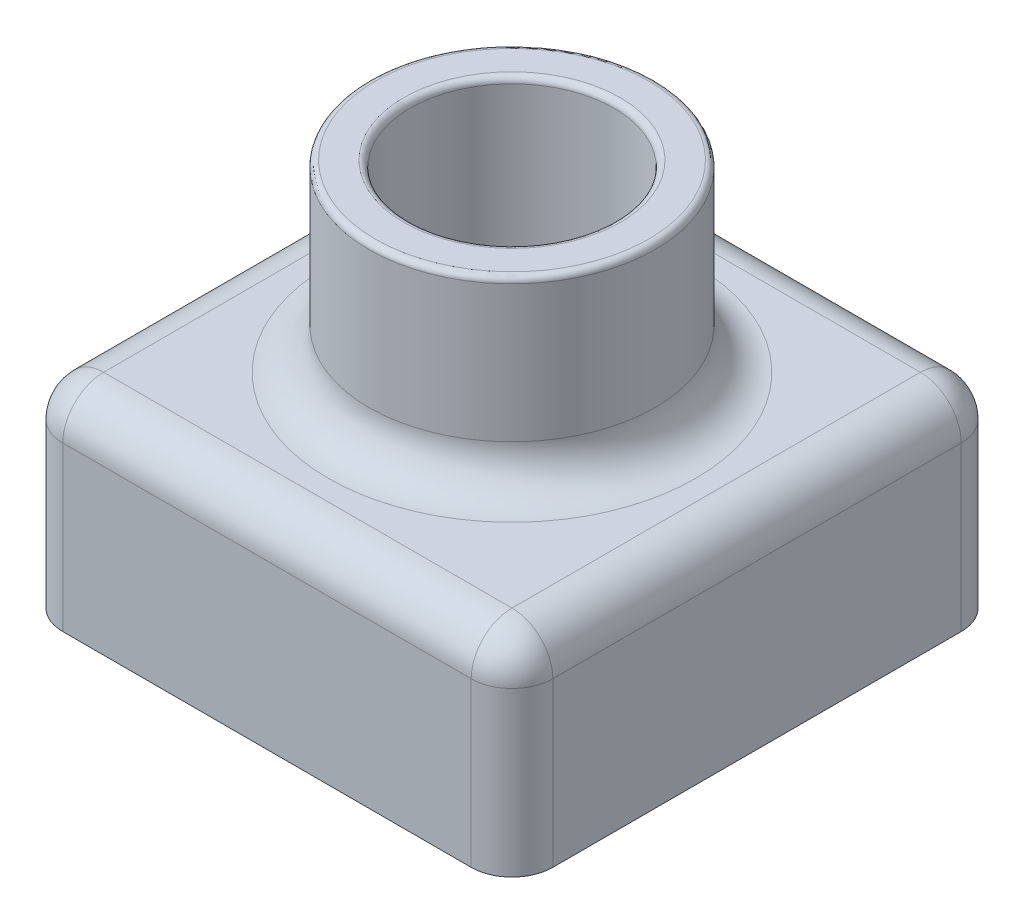
SolidWorks part; units mm, degrees
ref_plane "Front Plane" through (0, 0, 0) normal (0, 0, 1) x (1, 0, 0)
ref_plane "Top Plane" through (0, 0, 0) normal (0, 1, 0) x (1, 0, 0)
ref_plane "Right Plane" through (0, 0, 0) normal (1, 0, 0) x (0, 0, -1)
sketch "Sketch3" plane through (0, 0, 0) normal (0, 1, 0) x (1, 0, 0)
  line L1 (0, 0) -> (120, 0)
  line L2 (0, 0) -> (0, 120)
  line L3 (0, 120) -> (120, 120)
  line L4 (120, 0) -> (120, 120)
  dimension "D1" = 120
  dimension "D2" = 120
extrude "Boss-Extrude2" add sketch "Sketch3" along normal blind 50 contours L2 L1 L4 L3
sketch "Sketch4" plane through (0, 50, 0) normal (0, 1, 0) x (1, 0, 0)
  line L0 (0, 120) -> (120, 120) construction
  line L1 (120, 0) -> (120, 120) construction
  circle A0 centre (60, 60) radius 35
  dimension "D1" = 70
  dimension "D2" = 60
  dimension "D3" = 60
extrude "Boss-Extrude3" add sketch "Sketch4" along normal blind 45 contours A0
sketch "Sketch9" plane through (0, 95, 0) normal (0, 1, 0) x (1, 0, 0)
  circle A0 centre (60, 60) radius 25
  dimension "D1" = 50
extrude "Cut-Extrude3" cut sketch "Sketch9" against normal through all contours A0
fillet "Fillet4" radius 10 9 edges at (120, 50, -60) (60, 50, 0) (0, 50, -60) (60, 50, -120) (60, 50, -25) (120, 25, -120) (0, 25, -120) (0, 25, 0) (120, 25, 0)
fillet "Fillet5" radius 1.5 2 edges at (60, 95, -25) (60, 95, -35)
shell "Shell2" thickness 2
